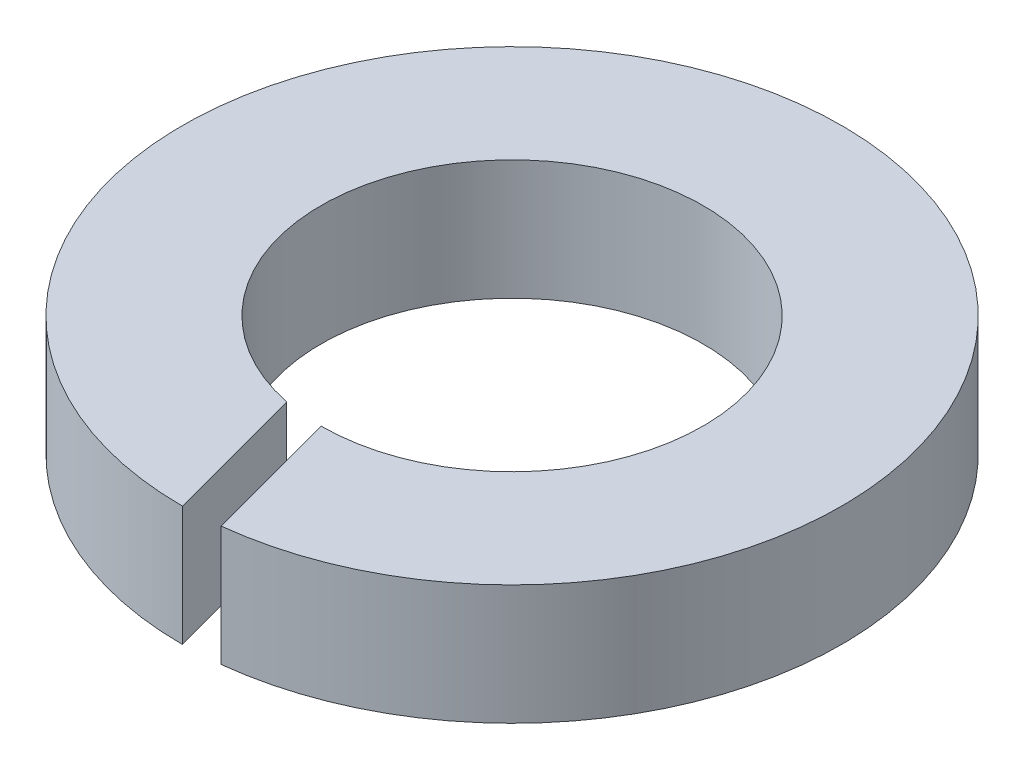
SolidWorks part; units mm, degrees
material "Нержавеющая сталь (ферритная)"
ref_plane "Спереди" through (0, 0, 0) normal (0, 0, 1) x (1, 0, 0)
ref_plane "Сверху" through (0, 0, 0) normal (0, 1, 0) x (1, 0, 0)
ref_plane "Справа" through (0, 0, 0) normal (1, 0, 0) x (0, 0, -1)
sketch "Эскиз1" plane through (0, 0, 0) normal (0, 1, 0) x (1, 0, 0)
  circle A0 centre (0, 0) radius 4.4
  circle A1 centre (0, 0) radius 2.55
  dimension "D1" = 8.8
  dimension "D2" = 5.1
extrude "Бобышка-Вытянуть1" add sketch "Эскиз1" along normal blind 1.6
sketch "Эскиз2" plane through (0, 1.6, 0) normal (0, 1, 0) x (1, 0, 0)
  line L0 (0, 0) -> (0, -50000) construction
  line L1 (0, -4.4) -> (-0.5095, -2.4986)
  line L2 (0, -2.55) -> (0.4884, -4.3728)
  circle A0 centre (0, 0) radius 4.4 construction
  circle A1 centre (0, 0) radius 2.55 construction
  arc A2 (0, -2.55) -> (-0.5095, -2.4986) centre (0, 0) cw
  arc A3 (0.4884, -4.3728) -> (0, -4.4) centre (0, 0) cw
  dimension "D1" = 15
  dimension "D2" = 15
extrude "Вырез-Вытянуть1" cut sketch "Эскиз2" against normal through all both and the other way through all
